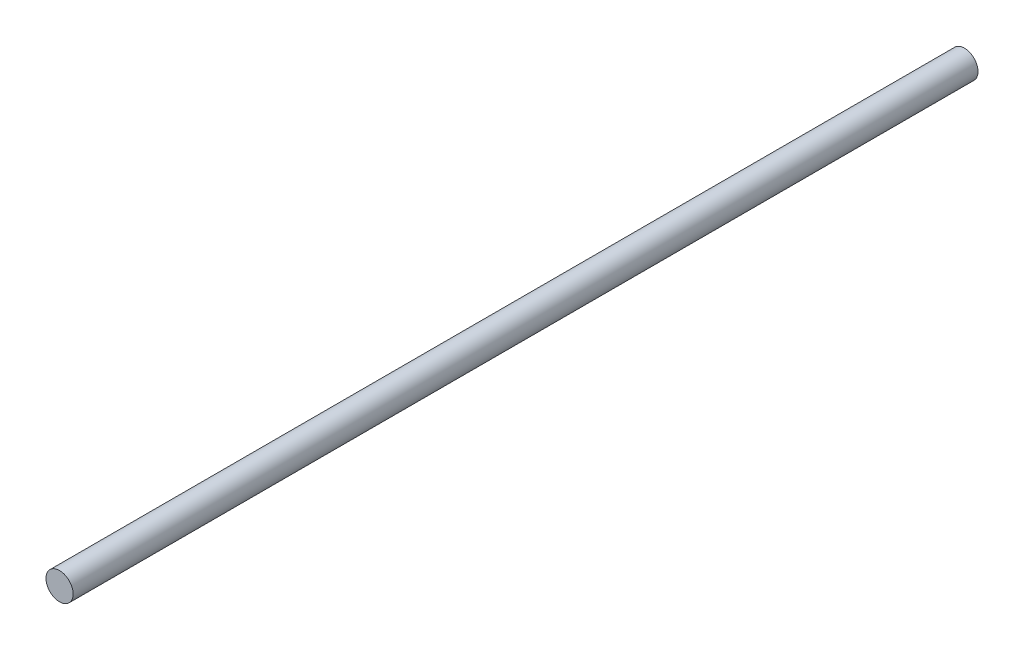
SolidWorks part; units mm, degrees
material "1060 Alloy"
ref_plane "Front Plane" through (0, 0, 0) normal (0, 0, 1) x (1, 0, 0)
ref_plane "Top Plane" through (0, 0, 0) normal (0, 1, 0) x (1, 0, 0)
ref_plane "Right Plane" through (0, 0, 0) normal (1, 0, 0) x (0, 0, -1)
sketch "Sketch1" plane through (0, 0, 0) normal (0, 0, 1) x (1, 0, 0)
  circle A0 centre (0, 0) radius 6
  dimension "D1" = 12
extrude "Boss-Extrude1" add sketch "Sketch1" along normal blind 400
